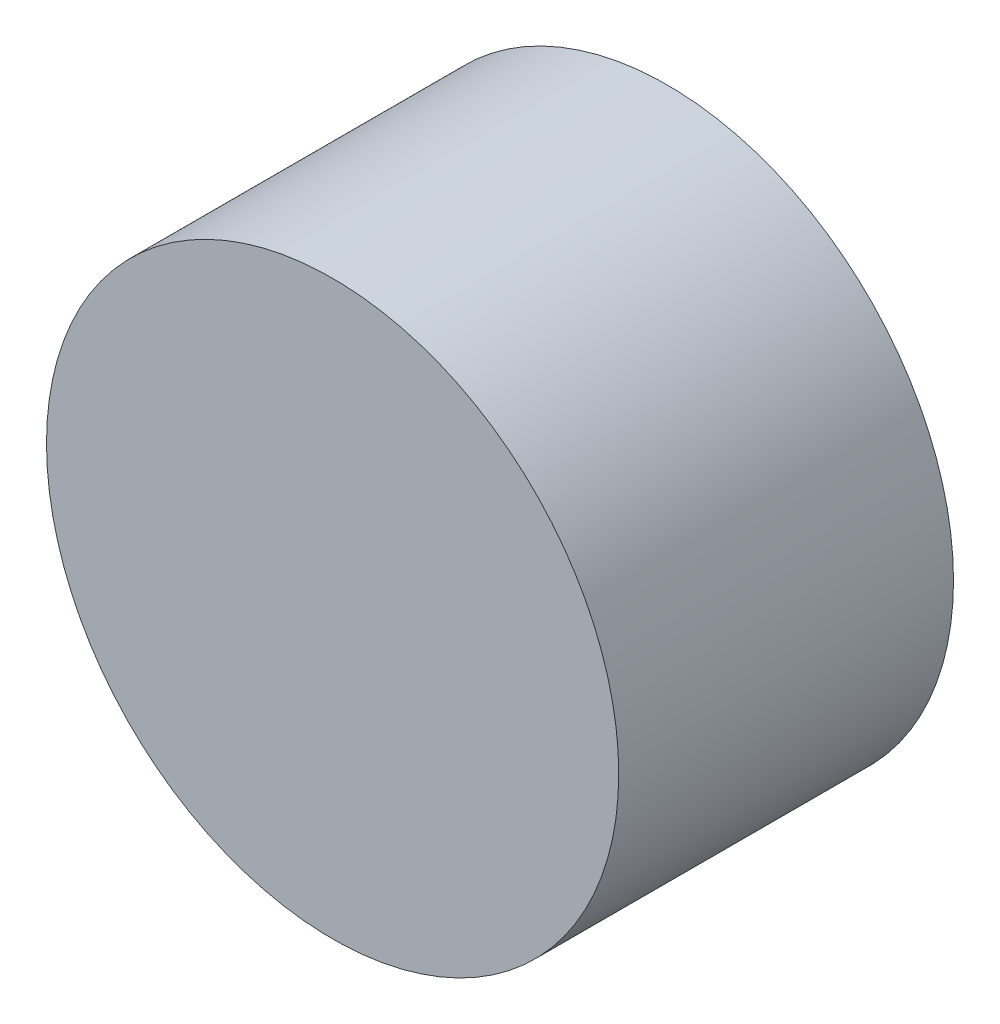
SolidWorks part; units mm, degrees
ref_plane "Front" through (0, 0, 0) normal (0, 0, 1) x (1, 0, 0)
ref_plane "Top" through (0, 0, 0) normal (0, 1, 0) x (1, 0, 0)
ref_plane "Right" through (0, 0, 0) normal (1, 0, 0) x (0, 0, -1)
sketch "Sketch1" plane through (0, 0, 0) normal (0, 0, 1) x (1, 0, 0)
  circle A0 centre (0, 0) radius 20.8407
  dimension "D1" = 41.6814
extrude "Extrude1" add sketch "Sketch1" along normal blind 24.384
